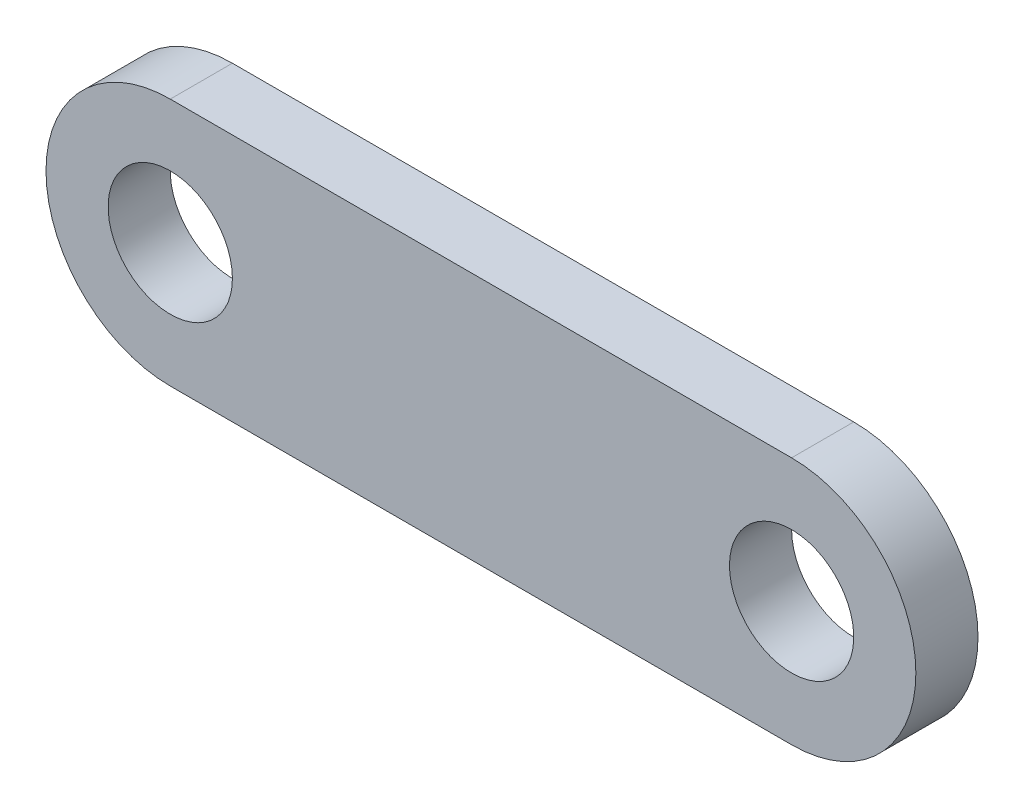
SolidWorks part; units mm, degrees
ref_plane "Front Plane" through (0, 0, 0) normal (0, 0, 1) x (1, 0, 0)
ref_plane "Top Plane" through (0, 0, 0) normal (0, 1, 0) x (1, 0, 0)
ref_plane "Right Plane" through (0, 0, 0) normal (1, 0, 0) x (0, 0, -1)
sketch "Sketch1" plane through (0, 0, 0) normal (0, 0, 1) x (1, 0, 0)
  line L0 (0, 0) -> (23.9594, 0) construction
  line L1 (23.9594, 0) -> (-18.4772, 0) construction
  line L2 (-18.4772, 0) -> (0, 0) construction
  line L3 (0, 0) -> (0, 19.4416) construction
  line L4 (0, 19.4416) -> (0, -15.7868) construction
  line L5 (0, 0) -> (20, 0) construction
  line L6 (0, 4) -> (20, 4)
  line L7 (0, -4) -> (20, -4)
  line L8 (10, 0) -> (10, 24.4162) construction
  line L9 (10, 24.4162) -> (10, -23.7056) construction
  arc A0 (0, 4) -> (0, -4) centre (0, 0) ccw
  arc A1 (20, -4) -> (20, 4) centre (20, 0) ccw
  circle A2 centre (0, 0) radius 2
  circle A3 centre (20, 0) radius 2
  point P4 (10, 0)
  dimension "D3" = 4
  dimension "D1" = 20
  dimension "D2" = 8
extrude "Boss-Extrude1" add sketch "Sketch1" along normal blind 2
